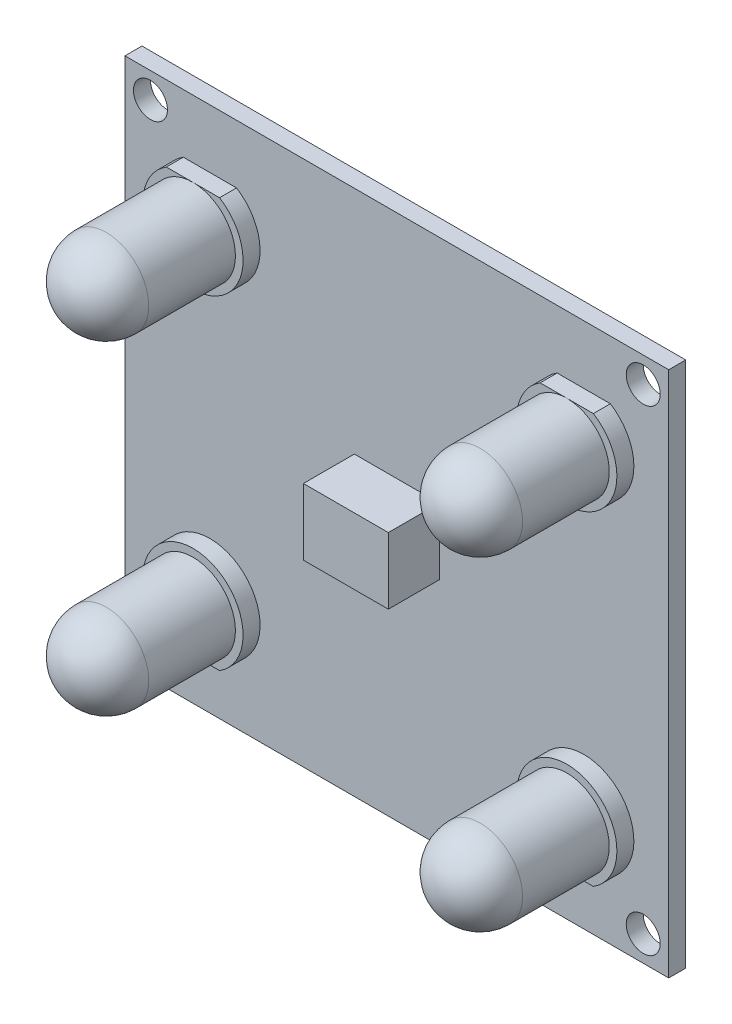
SolidWorks part; units mm, degrees
ref_plane "Alzado" through (0, 0, 0) normal (0, 0, 1) x (1, 0, 0)
ref_plane "Planta" through (0, 0, 0) normal (0, 1, 0) x (1, 0, 0)
ref_plane "Vista lateral" through (0, 0, 0) normal (1, 0, 0) x (0, 0, -1)
sketch "Sketch1" plane through (0, 0, 0) normal (0, 0, 1) x (1, 0, 0)
  line L1 (-22.1257, 18.3771) -> (9.8743, 18.3771)
  line L2 (-22.1257, 18.3771) -> (-22.1257, -6.6229)
  line L3 (-22.1257, -6.6229) -> (9.8743, -6.6229)
  line L4 (9.8743, 18.3771) -> (9.8743, -6.6229)
  dimension "D1" = 32
  dimension "D2" = 25
extrude "Boss-Extrude1" add sketch "Sketch1" along normal blind 1
sketch "Sketch2" plane through (0, 0, 1) normal (0, 0, 1) x (1, 0, 0)
  line L0 (-22.1257, -6.6229) -> (9.8743, -6.6229) construction
  line L1 (9.8743, 18.3771) -> (-22.1257, 18.3771) construction
  line L2 (-22.1257, 18.3771) -> (-22.1257, -6.6229) construction
  line L6 (-17.1257, 15.8771) -> (4.8743, -4.1229) construction
  line L7 (4.8743, 15.8771) -> (-17.1257, -4.1229) construction
  line L9 (-8.6257, 8.1499) -> (-3.6257, 8.1499)
  line L10 (-8.6257, 8.1499) -> (-8.6257, 3.6044)
  line L11 (-8.6257, 3.6044) -> (-3.6257, 3.6044)
  line L12 (-3.6257, 8.1499) -> (-3.6257, 3.6044)
  line L13 (-8.6257, 8.1499) -> (-3.6257, 3.6044) construction
  line L14 (-8.6257, 3.6044) -> (-3.6257, 8.1499) construction
  circle A0 centre (-17.1257, 15.8771) radius 2.5
  circle A1 centre (4.8743, 15.8771) radius 2.5
  circle A2 centre (-17.1257, -4.1229) radius 2.5
  circle A3 centre (4.8743, -4.1229) radius 2.5
  point P14 (-6.1257, 5.8771)
  dimension "D1" = 20
  dimension "D7" = 5
  dimension "D2" = 2.5
  dimension "D3" = 22
  dimension "D4" = 22
  dimension "D5" = 2.5
  dimension "D6" = 2.5
  dimension "D8" = 5
  dimension "D9" = 5
extrude "Boss-Extrude2" add sketch "Sketch2" along normal blind 8.7
sketch "Sketch3" plane through (0, 0, 9.7) normal (0, 0, 1) x (1, 0, 0)
  line L1 (-9.6819, 9.1718) -> (-2.5696, 9.1718)
  line L2 (-9.6819, 9.1718) -> (-9.6819, 2.5476)
  line L3 (-9.6819, 2.5476) -> (-2.5696, 2.5476)
  line L4 (-2.5696, 9.1718) -> (-2.5696, 2.5476)
  line L5 (-9.6819, 9.1718) -> (-2.5696, 2.5476) construction
  line L6 (-9.6819, 2.5476) -> (-2.5696, 9.1718) construction
  point P0 (-6.1257, 5.8597)
extrude "Cut-Extrude1" cut sketch "Sketch3" against normal blind 5.7
fillet "Fillet3" radius 0.5 4 edges at (-6.1257, 3.6044, 4) (-6.1257, 8.1499, 4) (-3.6257, 5.8771, 4) (-8.6257, 5.8771, 4)
fillet "Fillet4" radius 2.5 1 edges at (7.3743, 15.8771, 9.7)
fillet "Fillet5" radius 2.5 3 edges at (-14.6257, 15.8771, 9.7) (-14.6257, -4.1229, 9.7) (7.3743, -4.1229, 9.7)
sketch "Sketch4" plane through (0, 0, 1) normal (0, 0, 1) x (1, 0, 0)
  circle A13 centre (-17.1257, -4.1229) radius 2.5
  circle A14 centre (-17.1257, 15.8771) radius 2.5
  circle A15 centre (4.8743, 15.8771) radius 2.5
  circle A16 centre (4.8743, -4.1229) radius 2.5
extrude "Cut-Extrude2" cut sketch "Sketch4" along normal blind 10
sketch "Sketch5" plane through (0, 0, 1) normal (0, 0, 1) x (1, 0, 0)
  line L0 (-22.1257, 18.3771) -> (-22.1257, -6.6229) construction
  line L1 (9.8743, 18.3771) -> (-22.1257, 18.3771) construction
  line L2 (-22.1257, -6.6229) -> (9.8743, -6.6229) construction
  line L3 (9.8743, -6.6229) -> (9.8743, 18.3771) construction
  circle A0 centre (-17.1257, 15.4271) radius 2.95
  circle A1 centre (-17.1257, -3.6729) radius 2.95
  circle A2 centre (4.8743, 15.4271) radius 2.95
  circle A3 centre (4.8743, -3.6729) radius 2.95
  dimension "D1" = 5
  dimension "D3" = 2.95
  dimension "D2" = 2.95
  dimension "D4" = 5
extrude "Boss-Extrude3" add sketch "Sketch5" along normal blind 1 separate body
sketch "Sketch8" plane through (0, 0, 2) normal (0, 0, 1) x (1, 0, 0)
  circle A0 centre (-17.1257, 15.4271) radius 2.5
extrude "Boss-Extrude6" add sketch "Sketch8" along normal blind 7.6 separate body
sketch "Sketch9" plane through (0, 0, 2) normal (0, 0, 1) x (1, 0, 0)
  line L0 (-17.1257, 17.9271) -> (-15.2872, 17.9271)
  line L1 (-15.2872, 17.9271) -> (-15.4855, 18.6485)
  line L2 (-15.4855, 18.6485) -> (-19.1213, 18.6229)
  line L3 (-19.1213, 18.6229) -> (-19.1213, 17.9271)
  line L4 (-19.1213, 17.9271) -> (-17.1257, 17.9271)
  circle A0 centre (-17.1257, 15.4271) radius 2.5 construction
extrude "Cut-Extrude4" cut sketch "Sketch9" against normal blind 1
fillet "Fillet6" radius 2.5 1 edges at (-14.6257, 15.4271, 9.6)
sketch "Sketch13" plane through (0, 0, 2) normal (0, 0, 1) x (1, 0, 0)
  circle A0 centre (4.8743, 15.4271) radius 2.3676
  circle A1 centre (-17.1257, -3.6729) radius 2.5
  circle A2 centre (4.8743, -3.6729) radius 2.5
extrude "Boss-Extrude7" add sketch "Sketch13" along normal blind 7.6 separate body
fillet "Fillet7" radius 2.5 1 edges at (-14.6257, -3.6729, 9.6)
fillet "Fillet10" radius 2.5 1 edges at (7.3743, -3.6729, 9.6)
sketch "Sketch14" plane through (0, 0, 9.6) normal (0, 0, 1) x (1, 0, 0)
  circle A0 centre (4.8743, 15.4271) radius 2.3676
extrude "Cut-Extrude6" cut sketch "Sketch14" against normal blind 7.6
sketch "Sketch15" plane through (0, 0, 2) normal (0, 0, 1) x (1, 0, 0)
  circle A0 centre (4.8743, 15.4271) radius 2.5
extrude "Boss-Extrude9" add sketch "Sketch15" along normal blind 7.6 separate body
fillet "Fillet12" radius 2.5 1 edges at (7.3743, 15.4271, 9.6)
sketch "Sketch16" plane through (0, 0, 2) normal (0, 0, 1) x (1, 0, 0)
  line L1 (-15.5597, 17.9271) -> (9.7011, 17.9271)
  line L2 (-15.5597, 17.9271) -> (-15.5597, 19.2538)
  line L3 (-15.5597, 19.2538) -> (9.7011, 19.2538)
  line L4 (9.7011, 17.9271) -> (9.7011, 19.2538)
extrude "Cut-Extrude7" cut sketch "Sketch16" against normal blind 1
sketch "Sketch17" plane through (0, 0, 2) normal (0, 0, 1) x (1, 0, 0)
  line L1 (-21.5331, -6.1735) -> (9.1727, -6.1735)
  line L2 (-21.5331, -6.1735) -> (-21.5331, -7.8281)
  line L3 (-21.5331, -7.8281) -> (9.1727, -7.8281)
  line L4 (9.1727, -6.1735) -> (9.1727, -7.8281)
extrude "Cut-Extrude8" cut sketch "Sketch17" against normal blind 1
sketch "Sketch21" plane through (0, 0, 4) normal (0, 0, 1) x (1, 0, 0)
  line L1 (-8.6257, 8.1499) -> (-3.6257, 8.1499)
  line L2 (-8.6257, 8.1499) -> (-8.6257, 3.6044)
  line L3 (-8.6257, 3.6044) -> (-3.6257, 3.6044)
  line L4 (-3.6257, 8.1499) -> (-3.6257, 3.6044)
extrude "Cut-Extrude10" cut sketch "Sketch21" against normal up to surface (3 mm away) up to face at (-6.1257, 5.8771, 1)
sketch "Sketch22" plane through (0, 0, 1) normal (0, 0, 1) x (1, 0, 0)
  line L0 (-22.1257, 18.3771) -> (9.8743, -6.6229) construction
  line L1 (9.8743, 18.3771) -> (-22.1257, -6.6229) construction
  line L3 (-8.6257, 7.8303) -> (-3.6257, 7.8303)
  line L4 (-8.6257, 7.8303) -> (-8.6257, 3.924)
  line L5 (-8.6257, 3.924) -> (-3.6257, 3.924)
  line L6 (-3.6257, 7.8303) -> (-3.6257, 3.924)
  line L7 (-8.6257, 7.8303) -> (-3.6257, 3.924) construction
  line L8 (-8.6257, 3.924) -> (-3.6257, 7.8303) construction
  point P8 (-6.1257, 5.8771)
  dimension "D1" = 5
extrude "Boss-Extrude11" add sketch "Sketch22" along normal blind 3 separate body
sketch "Sketch24" plane through (0, 18.3771, 0) normal (0, 1, 0) x (1, 0, 0)
  line L1 (-22.1257, 0) -> (9.8743, 0)
  line L2 (-22.1257, 0) -> (-22.1257, -1)
  line L3 (-22.1257, -1) -> (9.8743, -1)
  line L4 (9.8743, 0) -> (9.8743, -1)
extrude "Boss-Extrude16" add sketch "Sketch24" along normal blind 3
sketch "Sketch26" plane through (0, -6.6229, 0) normal (0, -1, 0) x (1, 0, 0)
  line L1 (-22.1257, 1) -> (9.8743, 1)
  line L2 (-22.1257, 1) -> (-22.1257, 0)
  line L3 (-22.1257, 0) -> (9.8743, 0)
  line L4 (9.8743, 1) -> (9.8743, 0)
extrude "Boss-Extrude17" add sketch "Sketch26" along normal blind 3
sketch "Sketch27" plane through (0, 0, 0) normal (0, 0, -1) x (-1, 0, 0)
  line L0 (-9.8743, 21.3771) -> (22.1257, 21.3771) construction
  line L1 (-9.8743, -9.6229) -> (-9.8743, 21.3771) construction
  line L2 (22.1257, -9.6229) -> (-9.8743, -9.6229) construction
  line L3 (22.1257, 21.3771) -> (22.1257, -9.6229) construction
  circle A0 centre (-8.3743, 19.8771) radius 1
  circle A1 centre (-8.3743, -8.1229) radius 1
  circle A2 centre (20.6257, -8.1229) radius 1
  circle A3 centre (20.6257, 19.8771) radius 1
  dimension "D1" = 1.5
  dimension "D3" = 1.5
  dimension "D4" = 1.5
  dimension "D2" = 1.5
extrude "Cut-Extrude11" cut sketch "Sketch27" against normal blind 3
